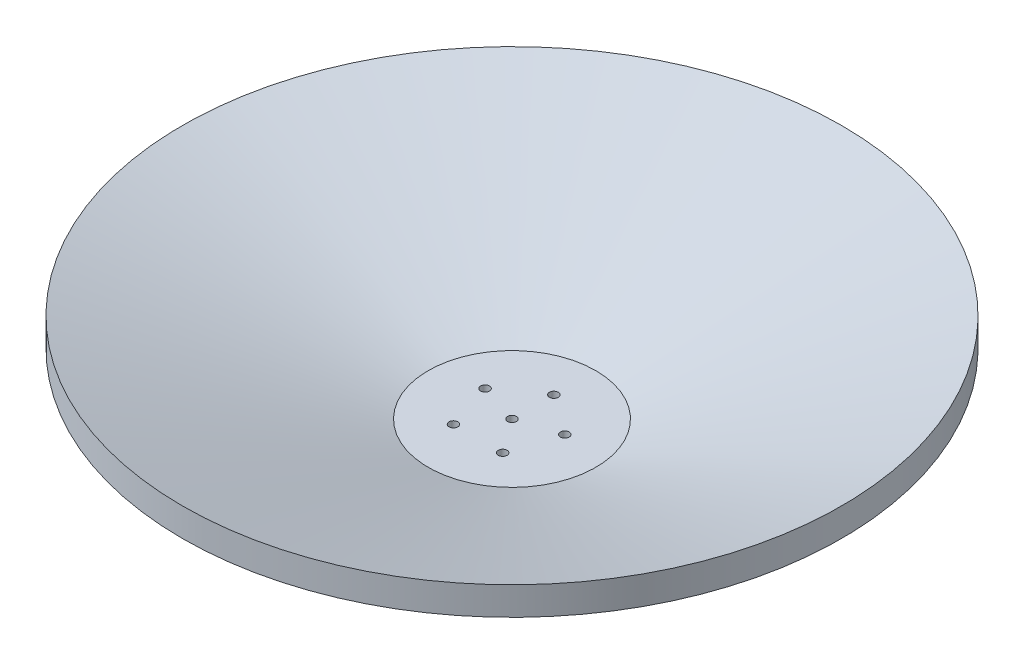
SolidWorks part; units mm, degrees
ref_plane "Front Plane" through (0, 0, 0) normal (0, 0, 1) x (1, 0, 0)
ref_plane "Top Plane" through (0, 0, 0) normal (0, 1, 0) x (1, 0, 0)
ref_plane "Right Plane" through (0, 0, 0) normal (1, 0, 0) x (0, 0, -1)
sketch "Sketch1" plane through (0, 0, 0) normal (0, 0, 1) x (1, 0, 0)
  line L0 (0, 0) -> (10, 0)
  line L1 (10, 0) -> (37.25, 9.9182)
  line L2 (0, 3) -> (9.471, 3)
  line L3 (9.471, 3) -> (36.2239, 12.7373)
  line L4 (9.471, 3) -> (36.2239, 12.7373) construction
  line L5 (36.2239, 12.7373) -> (37.25, 13.1107)
  line L6 (37.25, 13.1107) -> (37.25, 9.9182)
  line L7 (0, 0) -> (0, 3)
  dimension "D1" = 10
  dimension "D2" = 160
  dimension "D3" = 37.25
  dimension "D4" = 3
revolve "Revolve1" add sketch "Sketch1" angle 360 about L7
sketch "Sketch2" plane through (0, 3, 0) normal (0, 1, 0) x (1, 0, 0)
  line L0 (0, 0) -> (0, 9.471)
  circle A0 centre (0, 0) radius 0.5
  circle A1 centre (0, 0) radius 9.471 construction
  circle A2 centre (0, 4.7355) radius 0.5
  circle A3 centre (4.5037, 1.4634) radius 0.5
  circle A4 centre (2.7835, -3.8311) radius 0.5
  circle A5 centre (-2.7835, -3.8311) radius 0.5
  circle A6 centre (-4.5037, 1.4634) radius 0.5
  point P19 (0, 0)
  dimension "D1" = 5
extrude "Cut-Extrude1" cut sketch "Sketch2" against normal blind 18
